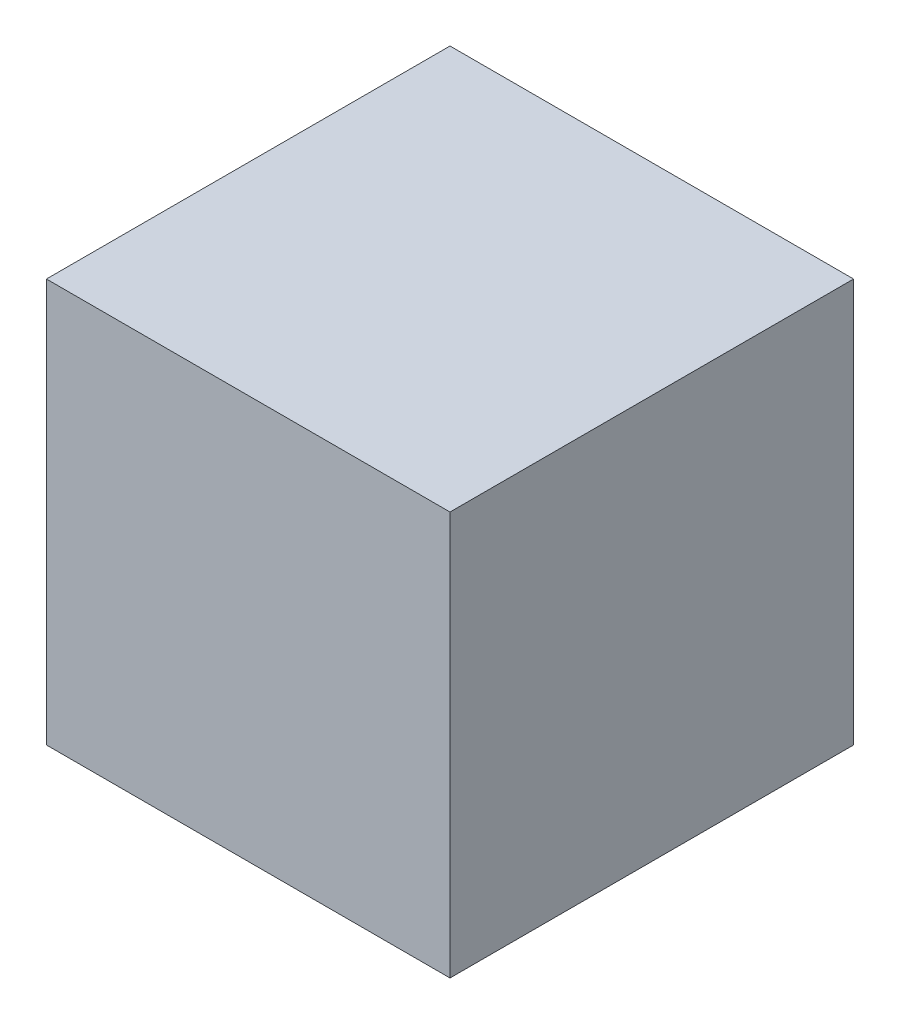
SolidWorks part; units mm, degrees
material "鎳"
ref_plane "前基準面" through (0, 0, 0) normal (0, 0, 1) x (1, 0, 0)
ref_plane "上基準面" through (0, 0, 0) normal (0, 1, 0) x (1, 0, 0)
ref_plane "右基準面" through (0, 0, 0) normal (1, 0, 0) x (0, 0, -1)
sketch "草圖1" plane through (0, 0, 0) normal (0, 0, 1) x (1, 0, 0)
  line L1 (-19.5, 19.5) -> (19.5, 19.5)
  line L2 (-19.5, 19.5) -> (-19.5, -19.5)
  line L3 (-19.5, -19.5) -> (19.5, -19.5)
  line L4 (19.5, 19.5) -> (19.5, -19.5)
  line L5 (-19.5, 19.5) -> (19.5, -19.5) construction
  line L6 (-19.5, -19.5) -> (19.5, 19.5) construction
  point P0 (0, 0)
  dimension "D1" = 39
  dimension "D2" = 39
extrude "填料-伸長1" add sketch "草圖1" along normal blind 39
sketch3d "URDF Reference"
  line L0 (0, 0, 0) -> (10, 0, 0) construction
  line L1 (0, 0, 0) -> (0, 0, -10) construction
  point P0 (0, 0, 0)
  point P1 (0, 0, 0)
